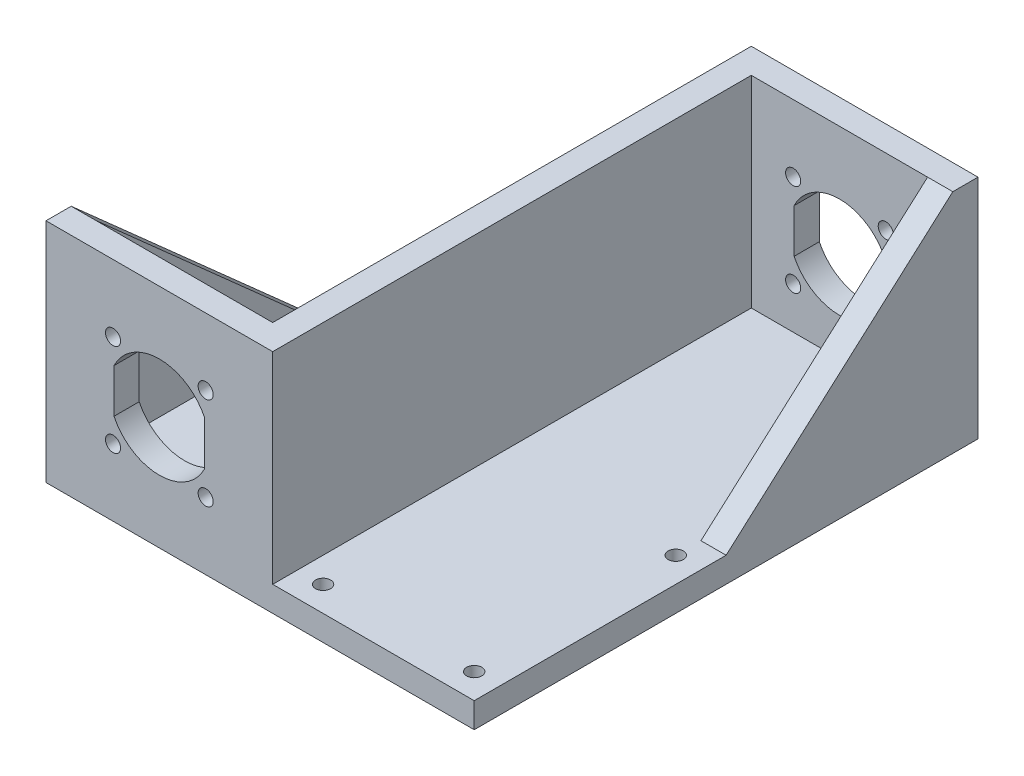
SolidWorks part; units mm, degrees
ref_plane "Plan de face" through (0, 0, 0) normal (0, 0, 1) x (1, 0, 0)
ref_plane "Plan de dessus" through (0, 0, 0) normal (0, 1, 0) x (1, 0, 0)
ref_plane "Plan de droite" through (0, 0, 0) normal (1, 0, 0) x (0, 0, -1)
sketch "Esquisse1" plane through (0, 0, 0) normal (0, 0, 1) x (1, 0, 0)
  line L0 (45, 0) -> (0, 45) construction
  line L1 (0, 0) -> (45, 0)
  line L2 (0, 0) -> (0, 45)
  line L3 (0, 45) -> (45, 45)
  line L4 (45, 0) -> (45, 45)
  line L5 (0, 0) -> (45, 45) construction
  line L6 (22.5, 45) -> (22.5, 0) construction
  line L7 (13.5, 26.8589) -> (13.5, 18.1411)
  line L8 (45, 22.5) -> (0, 22.5) construction
  line L9 (31.5, 26.8589) -> (31.5, 18.1411)
  arc A0 (13.5, 18.1411) -> (31.5, 18.1411) centre (22.5, 22.5) ccw
  circle A1 centre (31.6924, 31.6924) radius 1.5
  circle A2 centre (31.6924, 13.3076) radius 1.5
  circle A3 centre (13.3076, 13.3076) radius 1.5
  circle A4 centre (13.3076, 31.6924) radius 1.5
  arc A5 (31.5, 26.8589) -> (13.5, 26.8589) centre (22.5, 22.5) ccw
  dimension "D3" = 20
  dimension "D5" = 3
  dimension "D1" = 45
  dimension "D2" = 45
  dimension "D4" = 13
  dimension "D6" = 9
extrude "Extrusion1" add sketch "Esquisse1" along normal blind 5
sketch "Esquisse2" plane through (0, 0, 5) normal (0, 0, 1) x (1, 0, 0)
  line L0 (45, 0) -> (45, 45) construction
  line L1 (0, 0) -> (45, 0)
  line L2 (0, 0) -> (0, 5)
  line L3 (0, 5) -> (45, 5)
  line L4 (45, 0) -> (45, 5)
  dimension "D1" = 5
extrude "Extrusion2" add sketch "Esquisse2" along normal blind 95
sketch "Esquisse3" plane through (45, 0, 0) normal (1, 0, 0) x (0, 0, -1)
  line L0 (-5, 5) -> (-5, 45)
  line L1 (-5, 45) -> (-50, 5)
  line L2 (-100, 5) -> (-5, 5) construction
  line L3 (-50, 5) -> (-5, 5)
  dimension "D1" = 45
extrude "Extrusion3" add sketch "Esquisse3" against normal blind 5
sketch "Esquisse4" plane through (0, 0, 0) normal (-1, 0, 0) x (0, 0, 1)
  line L0 (5, 5) -> (5, 45)
  line L1 (5, 45) -> (100, 45)
  line L2 (100, 45) -> (100, 5)
  line L3 (100, 5) -> (5, 5)
extrude "Extrusion4" add sketch "Esquisse4" against normal blind 5
sketch "Esquisse5" plane through (0, 0, 0) normal (-1, 0, 0) x (0, 0, 1)
  line L0 (100, 45) -> (100, 0) construction
  line L1 (0, 0) -> (100, 0)
  line L2 (0, 0) -> (0, 5)
  line L3 (0, 5) -> (100, 5)
  line L4 (100, 0) -> (100, 5)
  dimension "D1" = 5
extrude "Extrusion5" add sketch "Esquisse5" along normal blind 40
sketch "Esquisse6" plane through (0, 0, 100) normal (0, 0, 1) x (1, 0, 0)
  line L0 (0, 5) -> (0, 45)
  line L1 (0, 45) -> (-40, 45)
  line L2 (-40, 45) -> (-40, 5)
  line L3 (-40, 5) -> (0, 5)
extrude "Extrusion6" add sketch "Esquisse6" against normal blind 5
sketch "Esquisse7" plane through (-40, 0, 0) normal (-1, 0, 0) x (0, 0, 1)
  line L0 (95, 5) -> (95, 45)
  line L1 (95, 45) -> (50, 5)
  line L2 (95, 5) -> (0, 5) construction
  line L3 (50, 5) -> (95, 5)
  dimension "D1" = 45
extrude "Extrusion7" add sketch "Esquisse7" against normal blind 5
sketch "Esquisse8" plane through (0, 0, 100) normal (0, 0, 1) x (1, 0, 0)
  line L0 (5, 5) -> (5, 0) construction
  line L1 (-40, 0) -> (45, 0) construction
  line L2 (5, 0) -> (-40, 45) construction
  line L3 (-40, 22.5) -> (5, 22.5) construction
  line L5 (-26.5, 18.1411) -> (-26.5, 26.8589)
  line L6 (-40, 0) -> (-40, 45) construction
  line L7 (5, 5) -> (5, 45) construction
  line L8 (5, 45) -> (-40, 0) construction
  line L9 (-8.5, 18.1411) -> (-8.5, 26.8589)
  line L10 (5, 45) -> (-40, 45) construction
  line L11 (-17.5, 45) -> (-17.5, 0) construction
  arc A0 (-26.5, 18.1411) -> (-8.5, 18.1411) centre (-17.5, 22.5) ccw
  circle A1 centre (-26.6924, 31.6924) radius 1.5
  circle A2 centre (-26.6924, 13.3076) radius 1.5
  circle A3 centre (-8.3076, 13.3076) radius 1.5
  circle A4 centre (-8.3076, 31.6924) radius 1.5
  arc A5 (-8.5, 26.8589) -> (-26.5, 26.8589) centre (-17.5, 22.5) ccw
  dimension "D1" = 20
  dimension "D2" = 3
  dimension "D3" = 13
  dimension "D4" = 9
extrude "Enlèv. mat.-Extru.1" cut sketch "Esquisse8" against normal up to next
sketch "Esquisse9" plane through (0, 5, 0) normal (0, 1, 0) x (-1, 0, 0)
  line L0 (-45, 100) -> (-5, 100) construction
  line L1 (-45, 100) -> (-45, 50) construction
  line L2 (40, 0) -> (0, 0) construction
  line L3 (40, 50) -> (40, 0) construction
  circle A0 centre (-40, 95) radius 1.5
  circle A1 centre (-10, 95) radius 1.5
  circle A2 centre (35, 5) radius 1.5
  circle A3 centre (5, 5) radius 1.5
  circle A4 centre (-40, 55) radius 1.5
  circle A5 centre (35, 45) radius 1.5
  dimension "D1" = 3
  dimension "D2" = 3
  dimension "D4" = 5
  dimension "D6" = 35
  dimension "D7" = 5
  dimension "D9" = 3
  dimension "D10" = 3
  dimension "D13" = 3
  dimension "D16" = 3
  dimension "D17" = 45
  dimension "D18" = 5
  dimension "D3" = 5
  dimension "D5" = 5
  dimension "D8" = 5
  dimension "D11" = 35
  dimension "D12" = 5
  dimension "D14" = 5
  dimension "D15" = 45
extrude "Enlèv. mat.-Extru.2" cut sketch "Esquisse9" against normal up to next
